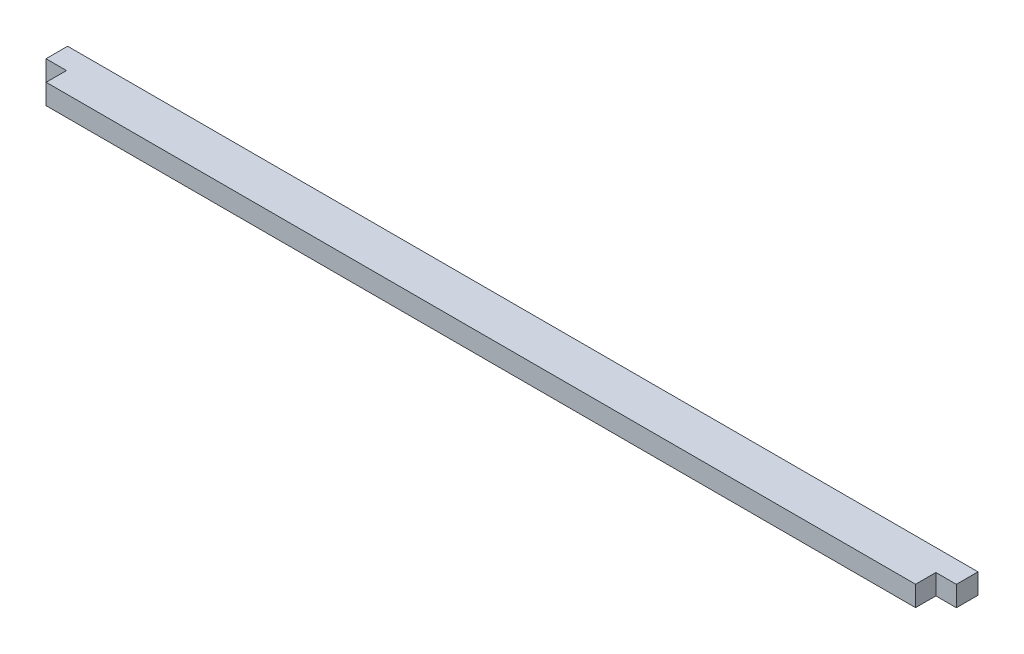
SolidWorks part; units mm, degrees
ref_plane "Front" through (0, 0, 0) normal (0, 0, 1) x (1, 0, 0)
ref_plane "Top" through (0, 0, 0) normal (0, 1, 0) x (1, 0, 0)
ref_plane "Right" through (0, 0, 0) normal (1, 0, 0) x (0, 0, -1)
sketch "Sketch2" plane through (0, 0, 0) normal (0, 1, 0) x (1, 0, 0)
  line L1 (3.2004, -6.35) -> (138.7919, -6.35)
  line L2 (0, -3.175) -> (0, 0)
  line L3 (0, 0) -> (141.9923, 0)
  line L4 (141.9923, -3.175) -> (141.9923, 0)
  line L9 (0, -3.175) -> (3.2004, -3.175)
  line L10 (3.2004, -6.35) -> (3.2004, -3.175)
  line L13 (141.9923, -3.175) -> (138.7919, -3.175)
  line L14 (138.7919, -6.35) -> (138.7919, -3.175)
  point P0 (0, 0)
  dimension "D1" = 141.9923
  dimension "D2" = 3.175
  dimension "D3" = 3.175
  dimension "D4" = 3.2004
extrude "Boss-Extrude1" add sketch "Sketch2" along normal blind 3.175
ref_plane "Plane1" [suppressed] through (0, 3.175, 0) normal (0, 1, 0) x (1, 0, 0)
sketch "Sketch3" [suppressed] plane through (0, 3.175, 0) normal (0, 1, 0) x (1, 0, 0)
  line L16 (123.8186, -3.2766) -> (123.8186, 0.1016)
  line L17 (123.8186, 0.1016) -> (-0.1016, 0.1016)
  line L18 (-0.1016, 0.1016) -> (-0.1016, -3.2766)
  line L19 (-0.1016, -3.2766) -> (3.0988, -3.2766)
  line L20 (3.0988, -3.2766) -> (3.0988, -6.4516)
  line L21 (3.0988, -6.4516) -> (120.6182, -6.4516)
  line L22 (120.6182, -6.4516) -> (120.6182, -3.2766)
  line L23 (120.6182, -3.2766) -> (123.8186, -3.2766)
  line L24 (123.8186, -3.2766) -> (123.8186, 0.1016)
  line L25 (123.8186, 0.1016) -> (-0.1016, 0.1016)
  line L26 (-0.1016, 0.1016) -> (-0.1016, -3.2766)
  line L27 (-0.1016, -3.2766) -> (3.0988, -3.2766)
  line L28 (3.0988, -3.2766) -> (3.0988, -6.4516)
  line L29 (3.0988, -6.4516) -> (120.6182, -6.4516)
  line L30 (120.6182, -6.4516) -> (120.6182, -3.2766)
  line L31 (120.6182, -3.2766) -> (123.8186, -3.2766)
  dimension "D1" = 0.1016
extrude "Boss-Extrude2" [suppressed] add sketch "Sketch3" against normal blind 3.175
ref_plane "Plane2" through (0, 3.175, 0) normal (0, 1, 0) x (1, 0, 0)
sketch "Sketch4" plane through (0, 3.175, 0) normal (0, 1, 0) x (1, 0, 0)
  line L16 (142.094, -3.2766) -> (142.094, 0.1016)
  line L17 (142.094, 0.1016) -> (-0.1016, 0.1016)
  line L18 (-0.1016, 0.1016) -> (-0.1016, -3.2766)
  line L19 (-0.1016, -3.2766) -> (3.0988, -3.2766)
  line L20 (3.0988, -3.2766) -> (3.0988, -6.4516)
  line L21 (3.0988, -6.4516) -> (138.8936, -6.4516)
  line L22 (138.8936, -6.4516) -> (138.8936, -3.2766)
  line L23 (138.8936, -3.2766) -> (142.094, -3.2766)
  line L24 (142.094, -3.2766) -> (142.094, 0.1016)
  line L25 (142.094, 0.1016) -> (-0.1016, 0.1016)
  line L26 (-0.1016, 0.1016) -> (-0.1016, -3.2766)
  line L27 (-0.1016, -3.2766) -> (3.0988, -3.2766)
  line L28 (3.0988, -3.2766) -> (3.0988, -6.4516)
  line L29 (3.0988, -6.4516) -> (138.8936, -6.4516)
  line L30 (138.8936, -6.4516) -> (138.8936, -3.2766)
  line L31 (138.8936, -3.2766) -> (142.094, -3.2766)
  dimension "D1" = 0.1016
extrude "Boss-Extrude3" add sketch "Sketch4" against normal blind 3.175
ref_plane "Plane3" [suppressed] through (0, 3.175, 0) normal (0, 1, 0) x (1, 0, 0)
sketch "Sketch5" [suppressed] plane through (0, 3.175, 0) normal (0, 1, 0) x (1, 0, 0)
  line L16 (132.9563, -3.2766) -> (132.9563, 0.1016)
  line L17 (132.9563, 0.1016) -> (-0.1016, 0.1016)
  line L18 (-0.1016, 0.1016) -> (-0.1016, -3.2766)
  line L19 (-0.1016, -3.2766) -> (3.0988, -3.2766)
  line L20 (3.0988, -3.2766) -> (3.0988, -6.4516)
  line L21 (3.0988, -6.4516) -> (129.7559, -6.4516)
  line L22 (129.7559, -6.4516) -> (129.7559, -3.2766)
  line L23 (129.7559, -3.2766) -> (132.9563, -3.2766)
  line L24 (132.9563, -3.2766) -> (132.9563, 0.1016)
  line L25 (132.9563, 0.1016) -> (-0.1016, 0.1016)
  line L26 (-0.1016, 0.1016) -> (-0.1016, -3.2766)
  line L27 (-0.1016, -3.2766) -> (3.0988, -3.2766)
  line L28 (3.0988, -3.2766) -> (3.0988, -6.4516)
  line L29 (3.0988, -6.4516) -> (129.7559, -6.4516)
  line L30 (129.7559, -6.4516) -> (129.7559, -3.2766)
  line L31 (129.7559, -3.2766) -> (132.9563, -3.2766)
  dimension "D1" = 0.1016
extrude "Boss-Extrude4" [suppressed] add sketch "Sketch5" against normal blind 3.175
equation "\"D1@Sketch2\"        = 4.62075 + 0.25 + 2 * ( 0.25 + 0.016 + ( 6 / 64 ) )"
